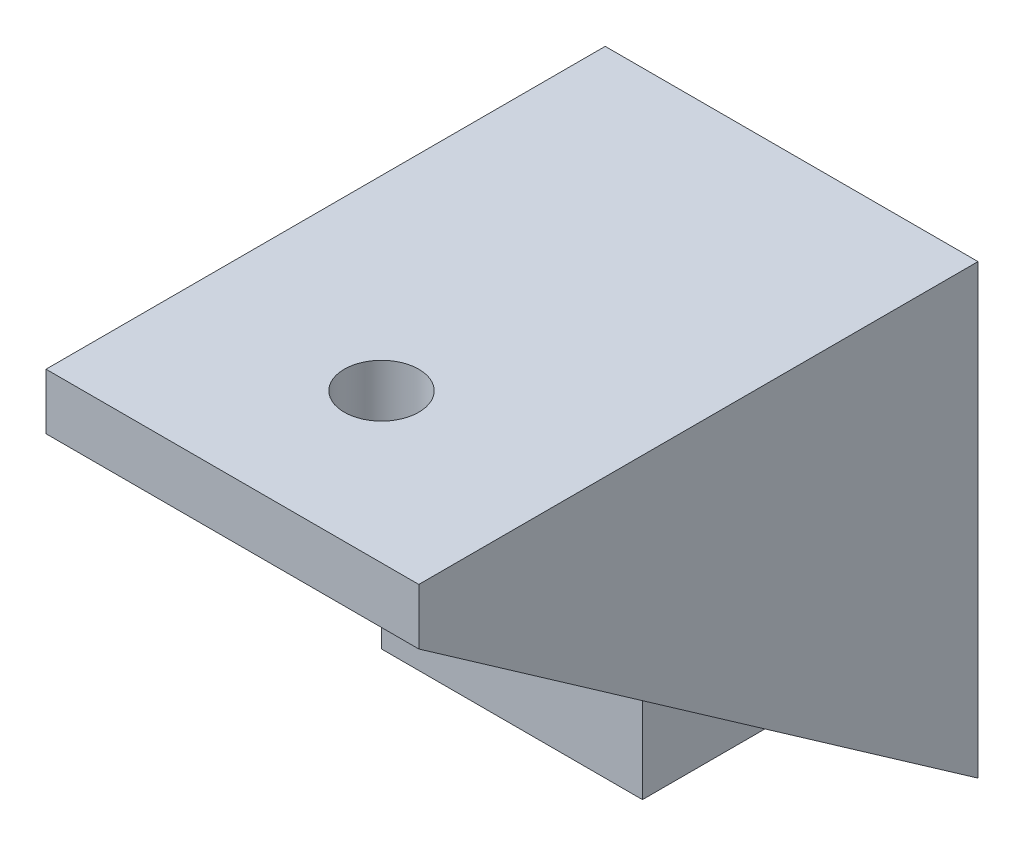
SolidWorks part; units mm, degrees
ref_plane "Front" through (0, 0, 0) normal (0, 0, 1) x (1, 0, 0)
ref_plane "Top" through (0, 0, 0) normal (0, 1, 0) x (1, 0, 0)
ref_plane "Right" through (0, 0, 0) normal (1, 0, 0) x (0, 0, -1)
sketch "Sketch1" plane through (0, 0, 0) normal (0, 0, 1) x (1, 0, 0)
  line L1 (-10, -12) -> (10, -12)
  line L2 (-10, -12) -> (-10, 12)
  line L3 (-10, 12) -> (10, 12)
  line L4 (10, -12) -> (10, 12)
  line L5 (-10, -12) -> (10, 12) construction
  line L6 (-10, 12) -> (10, -12) construction
  point P0 (0, 0)
  dimension "D1" = 24
  dimension "D2" = 20
extrude "Boss-Extrude1" add sketch "Sketch1" along normal blind 30
sketch "Sketch2" plane through (10, 0, 0) normal (1, 0, 0) x (0, 0, -1)
  line L0 (0, -12) -> (-30, 9)
  line L1 (-30, -12) -> (-30, 12) construction
  line L2 (-30, 12) -> (0, 12) construction
  line L3 (-30, 9) -> (-30, -12)
  line L4 (-30, -12) -> (0, -12)
  dimension "D1" = 3
extrude "Cut-Extrude1" cut sketch "Sketch2" against normal through all
sketch "Sketch3" plane through (0, 0, 30) normal (0, 0, 1) x (1, 0, 0)
  line L0 (-8, 10) -> (-8, -10)
  line L1 (-10, 12) -> (10, 12)
  line L2 (-10, 12) -> (-10, -12)
  line L3 (-10, -12) -> (10, -12)
  line L4 (10, 12) -> (10, -12)
  line L5 (-10, 12) -> (10, -12) construction
  line L6 (-10, -12) -> (10, 12) construction
  line L7 (-8, -10) -> (8, -10)
  line L8 (8, 10) -> (8, -10)
  line L9 (-8, 10) -> (8, 10)
  point P4 (0, 0)
  line M10 (-10, 9) -> (10, 9)
  dimension "D1" = 2
extrude "Cut-Extrude2" cut sketch "Sketch3" against normal blind 27 contours L8 L0 L7 M10
sketch "Sketch4" plane through (0, 0, 3) normal (0, 0, 1) x (1, 0, 0)
  line L1 (-7, -7) -> (7, -7)
  line L2 (-7, -7) -> (-7, 7)
  line L3 (-7, 7) -> (7, 7)
  line L4 (7, -7) -> (7, 7)
  line L5 (-7, -7) -> (7, 7) construction
  line L6 (-7, 7) -> (7, -7) construction
  point P0 (0, 0)
  dimension "D1" = 14
extrude "Boss-Extrude2" add sketch "Sketch4" along normal blind 12
sketch "Sketch5" plane through (0, 0, 0) normal (0, 0, -1) x (-1, 0, 0)
  circle A0 centre (0, 0) radius 1.6
  dimension "D1" = 3.2
extrude "Cut-Extrude3" cut sketch "Sketch5" against normal through all
sketch "Sketch6" plane through (0, 9, 0) normal (0, -1, 0) x (1, 0, 0)
  circle A0 centre (0, 22) radius 2
  dimension "D1" = 4
  dimension "D2" = 22
extrude "Cut-Extrude4" cut sketch "Sketch6" against normal through all
